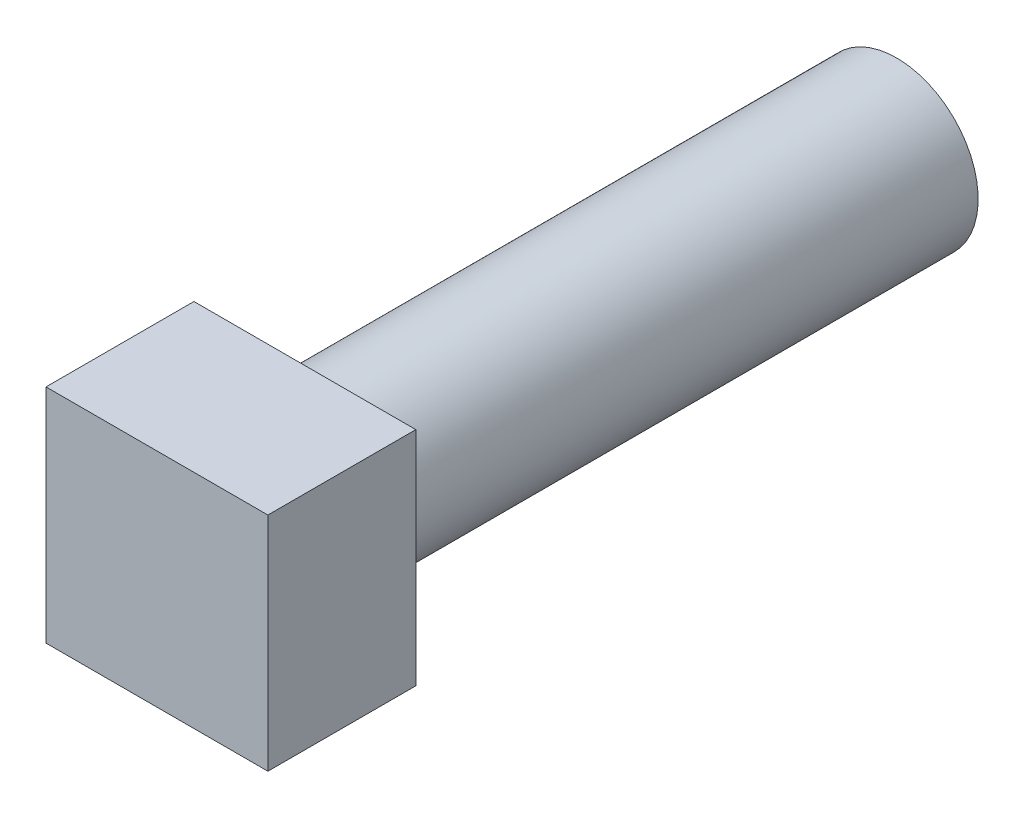
SolidWorks part; units mm, degrees
ref_plane "Front Plane" through (0, 0, 0) normal (0, 0, 1) x (1, 0, 0)
ref_plane "Top Plane" through (0, 0, 0) normal (0, 1, 0) x (1, 0, 0)
ref_plane "Right Plane" through (0, 0, 0) normal (1, 0, 0) x (0, 0, -1)
sketch "Sketch1" plane through (0, 0, 0) normal (0, 0, 1) x (1, 0, 0)
  line L1 (-4.7625, -4.7625) -> (4.7625, -4.7625)
  line L2 (-4.7625, -4.7625) -> (-4.7625, 4.7625)
  line L3 (-4.7625, 4.7625) -> (4.7625, 4.7625)
  line L4 (4.7625, -4.7625) -> (4.7625, 4.7625)
  line L5 (-4.7625, -4.7625) -> (4.7625, 4.7625) construction
  line L6 (-4.7625, 4.7625) -> (4.7625, -4.7625) construction
  point P0 (0, 0)
  dimension "D1" = 9.525
extrude "Boss-Extrude1" add sketch "Sketch1" along normal blind 6.35
sketch "Sketch2" plane through (0, 0, 0) normal (0, 0, -1) x (-1, 0, 0)
  circle A0 centre (0, 0) radius 3.5
  dimension "D1" = 7
extrude "Boss-Extrude2" add sketch "Sketch2" along normal blind 25.4
